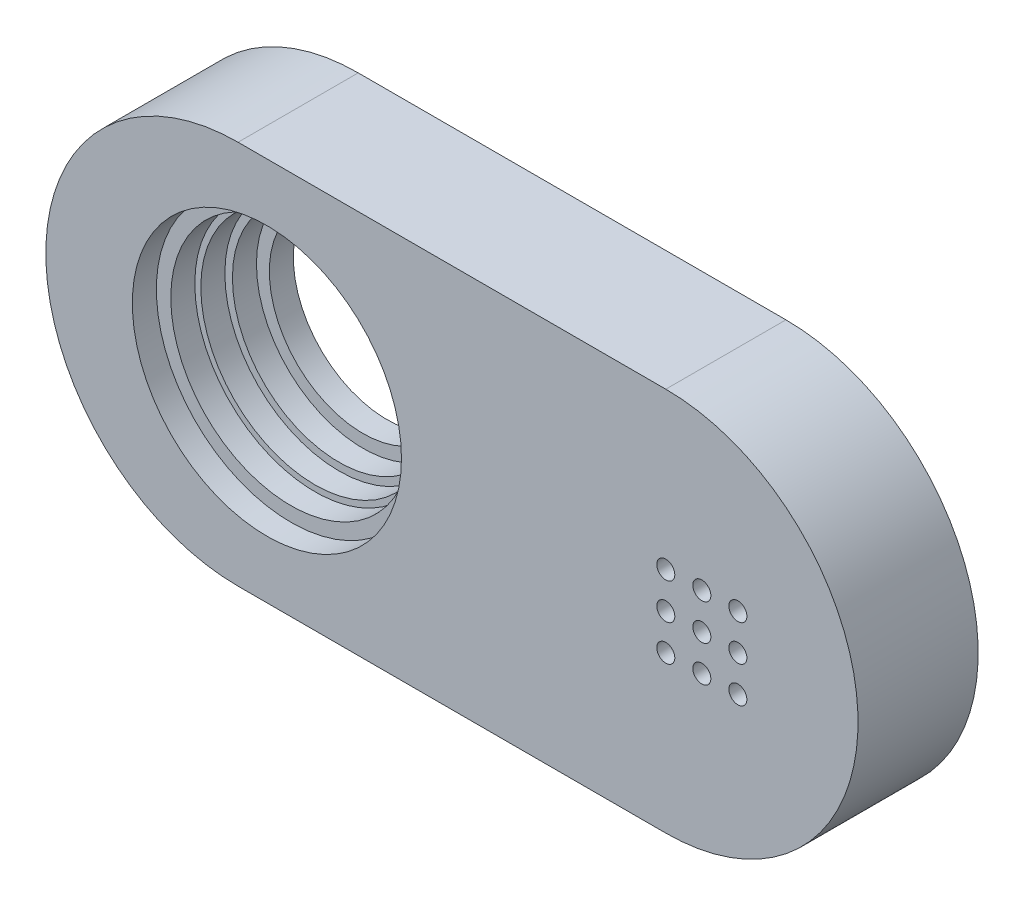
SolidWorks part; units mm, degrees
ref_plane "Front Plane" through (0, 0, 0) normal (0, 0, 1) x (1, 0, 0)
ref_plane "Top Plane" through (0, 0, 0) normal (0, 1, 0) x (1, 0, 0)
ref_plane "Right Plane" through (0, 0, 0) normal (1, 0, 0) x (0, 0, -1)
sketch "Sketch1" plane through (0, 0, 0) normal (0, 0, 1) x (1, 0, 0)
  line L0 (-8.9, 0) -> (8.9, 0) construction
  line L1 (-8.9, 8) -> (8.9, 8)
  line L2 (-8.9, -8) -> (8.9, -8)
  line L3 (0, 4.8795) -> (0, -3.8397) construction
  arc A0 (-8.9, 8) -> (-8.9, -8) centre (-8.9, 0) ccw
  arc A1 (8.9, -8) -> (8.9, 8) centre (8.9, 0) ccw
  point P3 (0, 0)
  dimension "D2" = 17.8
  dimension "D1" = 16
extrude "Boss-Extrude1" add sketch "Sketch1" along normal blind 5
sketch "Sketch2" plane through (0, 0, 5) normal (0, 0, 1) x (1, 0, 0)
  line L0 (0, 0) -> (-20.3647, 0) construction
  circle A0 centre (-7.7, 0) radius 3.9
  arc A1 (-8.9, 8) -> (-8.9, -8) centre (-8.9, 0) ccw construction
  point P6 (-16.9, 0)
  dimension "D1" = 7.8
  dimension "D2" = 9.2
extrude "Cut-Extrude1" cut sketch "Sketch2" against normal blind 5
sketch "Sketch3" plane through (0, 0, 5) normal (0, 0, 1) x (1, 0, 0)
  circle A0 centre (-7.7, 0) radius 4.435
  dimension "D1" = 8.87
extrude "Cut-Extrude2" cut sketch "Sketch3" against normal blind 4
sketch "Sketch4" plane through (0, 0, 5) normal (0, 0, 1) x (1, 0, 0)
  circle A0 centre (-7.7, 0) radius 4.75
  dimension "D1" = 9.5
extrude "Cut-Extrude3" cut sketch "Sketch4" against normal blind 3
sketch "Sketch5" plane through (0, 0, 5) normal (0, 0, 1) x (1, 0, 0)
  circle A0 centre (-7.7, 0) radius 5
  dimension "D1" = 10
extrude "Cut-Extrude4" cut sketch "Sketch5" against normal blind 2
sketch "Sketch6" plane through (0, 0, 5) normal (0, 0, 1) x (1, 0, 0)
  circle A0 centre (-7.7, 0) radius 5.6
  dimension "D1" = 11.2
extrude "Cut-Extrude5" cut sketch "Sketch6" against normal blind 1
sketch "Sketch7" plane through (0, 0, 5) normal (0, 0, 1) x (1, 0, 0)
  line L0 (-0.1318, 0) -> (15.89, 0) construction
  line L1 (0, 1.488) -> (0, -1.3868) construction
  circle A0 centre (10.4, 0) radius 0.375
  arc A1 (8.9, -8) -> (8.9, 8) centre (8.9, 0) ccw construction
  circle A2 centre (8.9, 0) radius 0.375
  circle A3 centre (11.9, 0) radius 0.375
  circle A4 centre (8.9, -1.5) radius 0.375
  circle A5 centre (10.4, -1.5) radius 0.375
  circle A6 centre (11.9, -1.5) radius 0.375
  circle A7 centre (8.9, 1.5) radius 0.375
  circle A8 centre (10.4, 1.5) radius 0.375
  circle A9 centre (11.9, 1.5) radius 0.375
  point P5 (16.9, 0)
  dimension "D1" = 0.75
  dimension "D2" = 6.5
  dimension "D3" = 1.5
  dimension "D4" = 1.5
  dimension "D5" = 1.5
  dimension "D6" = 1.5
  dimension "D7" = 1.5
extrude "Cut-Extrude6" cut sketch "Sketch7" against normal through all
